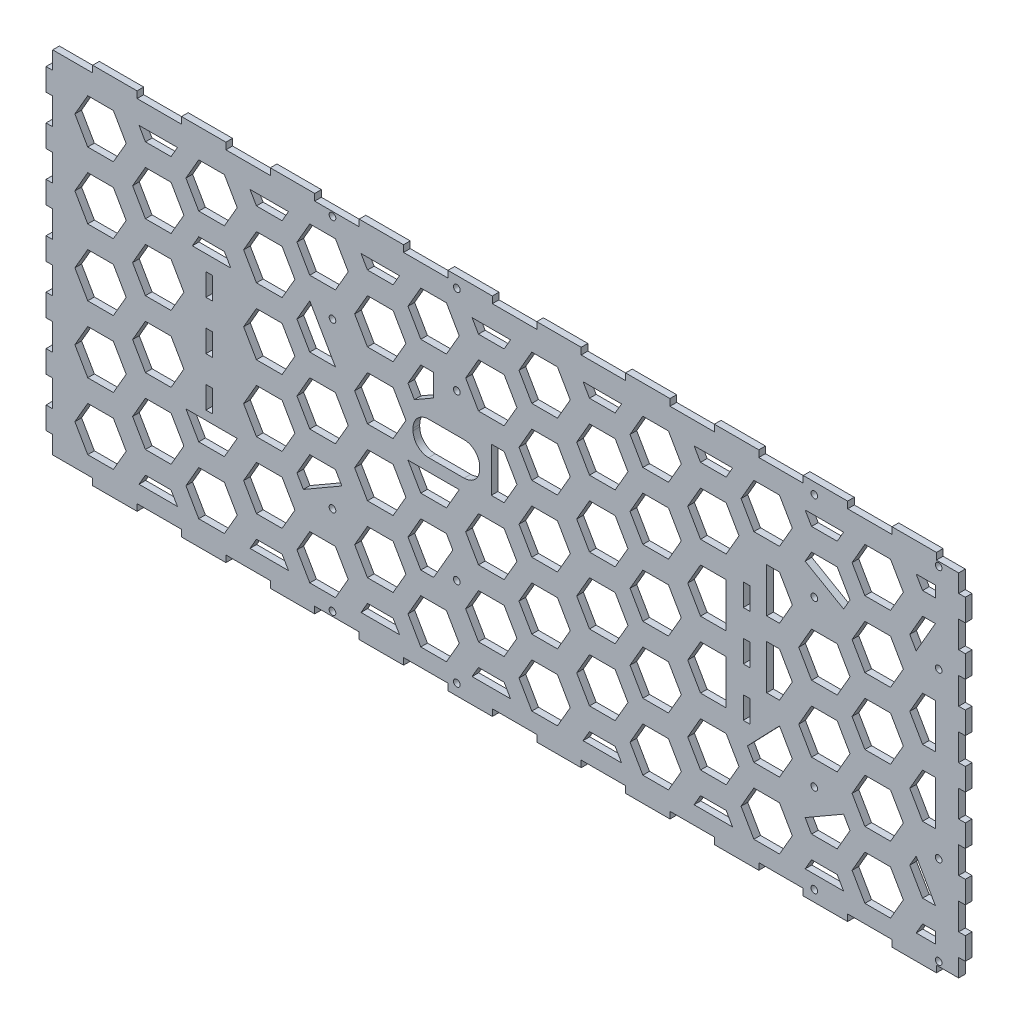
SolidWorks part; units mm, degrees
material "birch 3mm plywood"
ref_plane "Front Plane" through (0, 0, 0) normal (0, 0, 1) x (1, 0, 0)
ref_plane "Top Plane" through (0, 0, 0) normal (0, 1, 0) x (1, 0, 0)
ref_plane "Right Plane" through (0, 0, 0) normal (1, 0, 0) x (0, 0, -1)
sketch "Sketch1" plane through (0, 0, 152) normal (0, 0, 1) x (1, 0, 0)
  line L1 (-207, 82) -> (207, 82)
  line L2 (-207, 82) -> (-207, -82)
  line L3 (-207, -82) -> (207, -82)
  line L4 (207, 82) -> (207, -82)
  line L12 (200, -75) -> (-200, -75) construction
  line L13 (200, 75) -> (200, -75) construction
  line L14 (-200, -75) -> (-200, 75) construction
  line L15 (-200, 75) -> (200, 75) construction
  line L26 (-200, 0) -> (200, 0) construction
  line L31 (-200, 0) -> (200, 0) construction
  point P14 (0, 0)
  point P15 (0, 0)
  point P32 (-47.5, -25.9413)
  point P35 (256.981, -145.9413)
  point P38 (10.8894, 25.9413)
  point P51 (10.8894, -25.9413)
  point P54 (256.981, 145.9413)
  dimension "D1" = 7
  dimension "D2" = 7
  dimension "D3" = 7
  dimension "D4" = 7
  dimension "D5" = 150
  dimension "D6" = 400
extrude "Boss-Extrude1" add sketch "Sketch1" along normal blind 3
sketch "Sketch2" plane through (-207, 0, 0) normal (-1, 0, 0) x (0, 0, 1)
  line L7 (155, -82) -> (152, -82)
  line L8 (152, -82) -> (152, -71)
  line L9 (152, 82) -> (155, 82)
  line L10 (155, 82) -> (155, 71)
  line L11 (152, -61) -> (152, -49)
  line L12 (155, -71) -> (155, -82)
  line L13 (155, -49) -> (155, -61)
  line L14 (152, -39) -> (152, -27)
  line L15 (152, -17) -> (152, -5)
  line L16 (155, -27) -> (155, -39)
  line L17 (155, -5) -> (155, -17)
  line L18 (152, 5) -> (152, 17)
  line L19 (152, 27) -> (152, 39)
  line L20 (155, 17) -> (155, 5)
  line L21 (155, 39) -> (155, 27)
  line L22 (152, 49) -> (152, 61)
  line L23 (152, 71) -> (152, 82)
  line L24 (155, 61) -> (155, 49)
  line L76 (132.5, 88.6) -> (132.5, 93.6)
  line L77 (132.5, 88.6) -> (132.5, 93.6)
  line L78 (129.5, 98.6) -> (128.8771, 98.6)
  line L79 (129.5, 98.6) -> (128.8771, 98.6)
  line L80 (129.5, 82) -> (129.5, 88.6)
  line L81 (129.5, 82) -> (129.5, 88.6)
  line L82 (129.5, 88.6) -> (132.5, 88.6)
  line L83 (129.5, 88.6) -> (132.5, 88.6)
  line L85 (16, 82) -> (16, -82)
  line L102 (129.5, -82) -> (133, -82)
  line L103 (133, -82) -> (133, -79)
  line L104 (133, -79) -> (145, -79)
  line L105 (145, -79) -> (145, -82)
  line L106 (145, -82) -> (155, -82)
  line L107 (155, -82) -> (155, -71)
  line L108 (155, -71) -> (152, -71)
  line L109 (152, -71) -> (152, -61)
  line L110 (152, -61) -> (155, -61)
  line L111 (155, -61) -> (155, -49)
  line L112 (155, -49) -> (152, -49)
  line L113 (152, -49) -> (152, -39)
  line L114 (152, -39) -> (155, -39)
  line L115 (155, -39) -> (155, -27)
  line L116 (155, -27) -> (152, -27)
  line L117 (152, -27) -> (152, -17)
  line L118 (152, -17) -> (155, -17)
  line L119 (155, -17) -> (155, -5)
  line L120 (155, -5) -> (152, -5)
  line L121 (152, -5) -> (152, 5)
  line L122 (152, 5) -> (155, 5)
  line L123 (155, 5) -> (155, 17)
  line L124 (155, 17) -> (152, 17)
  line L125 (152, 17) -> (152, 27)
  line L126 (152, 27) -> (155, 27)
  line L127 (155, 27) -> (155, 39)
  line L128 (155, 39) -> (152, 39)
  line L129 (152, 39) -> (152, 49)
  line L130 (152, 49) -> (155, 49)
  line L131 (155, 49) -> (155, 61)
  line L132 (155, 61) -> (152, 61)
  line L133 (152, 61) -> (152, 71)
  line L134 (152, 71) -> (155, 71)
  line L135 (155, 71) -> (155, 82)
  line L136 (155, 82) -> (145, 82)
  line L137 (145, 82) -> (145, 79)
  line L138 (145, 79) -> (133, 79)
  line L139 (133, 79) -> (133, 82)
  line L140 (133, 82) -> (129.5, 82)
  line L184 (155, -71) -> (152, -71)
  line L186 (152, -61) -> (155, -61)
  line L188 (155, -49) -> (152, -49)
  line L190 (152, -39) -> (155, -39)
  line L192 (155, -27) -> (152, -27)
  line L194 (152, -17) -> (155, -17)
  line L196 (155, -5) -> (152, -5)
  line L198 (152, 5) -> (155, 5)
  line L200 (155, 17) -> (152, 17)
  line L202 (152, 27) -> (155, 27)
  line L204 (155, 39) -> (152, 39)
  line L206 (152, 49) -> (155, 49)
  line L208 (155, 61) -> (152, 61)
  line L210 (152, 71) -> (155, 71)
  line L297 (132.5, 93.6) -> (129.5, 93.6)
  line L298 (132.5, 93.6) -> (129.5, 93.6)
  line L299 (129.5, 93.6) -> (129.5, 98.6)
  line L300 (129.5, 93.6) -> (129.5, 98.6)
  line L301 (128.8771, -98.6) -> (129.5, -98.6)
  line L302 (128.8771, -98.6) -> (129.5, -98.6)
  line L303 (129.5, -98.6) -> (129.5, -93.6)
  line L304 (129.5, -98.6) -> (129.5, -93.6)
  line L305 (129.5, -93.6) -> (132.5, -93.6)
  line L306 (129.5, -93.6) -> (132.5, -93.6)
  line L307 (132.5, -93.6) -> (132.5, -88.6)
  line L308 (132.5, -93.6) -> (132.5, -88.6)
  line L309 (132.5, -88.6) -> (129.5, -88.6)
  line L310 (132.5, -88.6) -> (129.5, -88.6)
  line L311 (129.5, -88.6) -> (129.5, -82)
  line L312 (129.5, -88.6) -> (129.5, -82)
  arc A4 (128.8771, 98.6) -> (16, 82) centre (128.8771, -293.4723) ccw
  arc A5 (128.8771, 98.6) -> (16, 82) centre (128.8771, -293.4723) ccw
  arc A6 (16, -82) -> (128.8771, -98.6) centre (128.8771, 293.4723) ccw
  arc A7 (16, -82) -> (128.8771, -98.6) centre (128.8771, 293.4723) ccw
  line M77 (152, 82) -> (152, -82)
  line M78 (152, -82) -> (155, -82)
  line M79 (155, -82) -> (155, 82)
  line M80 (155, 82) -> (152, 82)
  dimension "D1" = 0
extrude "Cut-Extrude1" cut sketch "Sketch2" against normal blind 3 contours L184 M79 M77 M78 | L188 L186 M79 M77 | L192 L190 M79 M77 | L196 L194 M79 M77 | L200 L198 M79 M77 | L204 L202 M79 M77 | L208 L206 M79 M77 | L210 M77 M79 M80
mirror "Mirror1" about plane through (0, 0, 0) normal (1, 0, 0) of "Cut-Extrude1"
sketch "Sketch3" plane through (0, 82, 0) normal (0, 1, 0) x (1, 0, 0)
  line L92 (174, -152) -> (194, -152)
  line L93 (194, -152) -> (194, -155)
  line L94 (194, -155) -> (204, -155)
  line L97 (207, -45) -> (204, -45)
  line L120 (204, -16) -> (-204, -16)
  line L123 (-204, -45) -> (-207, -45)
  line L146 (-204, -155) -> (-186, -155)
  line L147 (-186, -155) -> (-186, -152)
  line L148 (-186, -152) -> (-166, -152)
  line L149 (-166, -152) -> (-166, -155)
  line L150 (-166, -155) -> (-146, -155)
  line L151 (-146, -155) -> (-146, -152)
  line L152 (-146, -152) -> (-126, -152)
  line L153 (-126, -152) -> (-126, -155)
  line L154 (-126, -155) -> (-106, -155)
  line L155 (-106, -155) -> (-106, -152)
  line L156 (-106, -152) -> (-86, -152)
  line L157 (-86, -152) -> (-86, -155)
  line L158 (-86, -155) -> (-66, -155)
  line L159 (-66, -155) -> (-66, -152)
  line L160 (-66, -152) -> (-46, -152)
  line L161 (-46, -152) -> (-46, -155)
  line L162 (-46, -155) -> (-26, -155)
  line L163 (-26, -155) -> (-26, -152)
  line L164 (-26, -152) -> (-6, -152)
  line L165 (-6, -152) -> (-6, -155)
  line L166 (-6, -155) -> (14, -155)
  line L167 (14, -155) -> (14, -152)
  line L168 (14, -152) -> (34, -152)
  line L169 (34, -152) -> (34, -155)
  line L170 (34, -155) -> (54, -155)
  line L171 (54, -155) -> (54, -152)
  line L172 (54, -152) -> (74, -152)
  line L173 (74, -152) -> (74, -155)
  line L174 (74, -155) -> (94, -155)
  line L175 (94, -155) -> (94, -152)
  line L176 (94, -152) -> (114, -152)
  line L177 (114, -152) -> (114, -155)
  line L178 (114, -155) -> (134, -155)
  line L179 (134, -155) -> (134, -152)
  line L180 (134, -152) -> (154, -152)
  line L181 (154, -152) -> (154, -155)
  line L182 (154, -155) -> (174, -155)
  line L183 (174, -155) -> (174, -152)
  line L184 (174, -152) -> (194, -152)
  line L185 (194, -152) -> (194, -155)
  line L186 (194, -155) -> (204, -155)
  line L212 (204, -16) -> (-204, -16)
  line L238 (-204, -155) -> (-186, -155)
  line L239 (-186, -155) -> (-186, -152)
  line L240 (-186, -152) -> (-166, -152)
  line L241 (-166, -152) -> (-166, -155)
  line L242 (-166, -155) -> (-146, -155)
  line L243 (-146, -155) -> (-146, -152)
  line L244 (-146, -152) -> (-126, -152)
  line L245 (-126, -152) -> (-126, -155)
  line L246 (-126, -155) -> (-106, -155)
  line L247 (-106, -155) -> (-106, -152)
  line L248 (-106, -152) -> (-86, -152)
  line L249 (-86, -152) -> (-86, -155)
  line L250 (-86, -155) -> (-66, -155)
  line L251 (-66, -155) -> (-66, -152)
  line L252 (-66, -152) -> (-46, -152)
  line L253 (-46, -152) -> (-46, -155)
  line L254 (-46, -155) -> (-26, -155)
  line L255 (-26, -155) -> (-26, -152)
  line L256 (-26, -152) -> (-6, -152)
  line L257 (-6, -152) -> (-6, -155)
  line L258 (-6, -155) -> (14, -155)
  line L259 (14, -155) -> (14, -152)
  line L260 (14, -152) -> (34, -152)
  line L261 (34, -152) -> (34, -155)
  line L262 (34, -155) -> (54, -155)
  line L263 (54, -155) -> (54, -152)
  line L264 (54, -152) -> (74, -152)
  line L265 (74, -152) -> (74, -155)
  line L266 (74, -155) -> (94, -155)
  line L267 (94, -155) -> (94, -152)
  line L268 (94, -152) -> (114, -152)
  line L269 (114, -152) -> (114, -155)
  line L270 (114, -155) -> (134, -155)
  line L271 (134, -155) -> (134, -152)
  line L272 (134, -152) -> (154, -152)
  line L273 (154, -152) -> (154, -155)
  line L274 (154, -155) -> (174, -155)
  line L275 (174, -155) -> (174, -152)
  line L576 (-204, -45) -> (-207, -45)
  line L577 (-207, -45) -> (-207, -57)
  line L578 (-207, -45) -> (-207, -57)
  line L579 (-207, -57) -> (-204, -57)
  line L580 (-207, -57) -> (-204, -57)
  line L581 (-204, -57) -> (-204, -67)
  line L582 (-204, -57) -> (-204, -67)
  line L583 (-204, -67) -> (-207, -67)
  line L584 (-204, -67) -> (-207, -67)
  line L585 (-207, -67) -> (-207, -79)
  line L586 (-207, -67) -> (-207, -79)
  line L587 (-207, -79) -> (-204, -79)
  line L588 (-207, -79) -> (-204, -79)
  line L589 (-204, -79) -> (-204, -89)
  line L590 (-204, -79) -> (-204, -89)
  line L591 (-204, -89) -> (-207, -89)
  line L592 (-204, -89) -> (-207, -89)
  line L593 (-207, -89) -> (-207, -101)
  line L594 (-207, -89) -> (-207, -101)
  line L595 (-207, -101) -> (-204, -101)
  line L596 (-207, -101) -> (-204, -101)
  line L597 (-204, -101) -> (-204, -111)
  line L598 (-204, -101) -> (-204, -111)
  line L599 (-204, -111) -> (-207, -111)
  line L600 (-204, -111) -> (-207, -111)
  line L601 (-207, -111) -> (-207, -123)
  line L602 (-207, -111) -> (-207, -123)
  line L603 (-207, -123) -> (-204, -123)
  line L604 (-207, -123) -> (-204, -123)
  line L605 (-204, -123) -> (-204, -133)
  line L606 (-204, -123) -> (-204, -133)
  line L607 (-204, -133) -> (-207, -133)
  line L608 (-204, -133) -> (-207, -133)
  line L609 (-207, -133) -> (-207, -145)
  line L610 (-207, -133) -> (-207, -145)
  line L611 (-207, -145) -> (-204, -145)
  line L612 (-207, -145) -> (-204, -145)
  line L613 (-204, -145) -> (-204, -155)
  line L614 (-204, -145) -> (-204, -155)
  line L615 (-204, -16) -> (-204, -23)
  line L616 (-204, -16) -> (-204, -23)
  line L617 (-204, -23) -> (-207, -23)
  line L618 (-204, -23) -> (-207, -23)
  line L619 (-207, -23) -> (-207, -35)
  line L620 (-207, -23) -> (-207, -35)
  line L621 (-207, -35) -> (-204, -35)
  line L622 (-207, -35) -> (-204, -35)
  line L623 (-204, -35) -> (-204, -45)
  line L624 (-204, -35) -> (-204, -45)
  line L741 (207, -45) -> (204, -45)
  line L742 (204, -45) -> (204, -35)
  line L743 (204, -45) -> (204, -35)
  line L744 (204, -35) -> (207, -35)
  line L745 (204, -35) -> (207, -35)
  line L746 (207, -35) -> (207, -23)
  line L747 (207, -35) -> (207, -23)
  line L748 (207, -23) -> (204, -23)
  line L749 (207, -23) -> (204, -23)
  line L750 (204, -23) -> (204, -16)
  line L751 (204, -23) -> (204, -16)
  line L752 (204, -155) -> (204, -145)
  line L753 (204, -155) -> (204, -145)
  line L754 (204, -145) -> (207, -145)
  line L755 (204, -145) -> (207, -145)
  line L756 (207, -145) -> (207, -133)
  line L757 (207, -145) -> (207, -133)
  line L758 (207, -133) -> (204, -133)
  line L759 (207, -133) -> (204, -133)
  line L760 (204, -133) -> (204, -123)
  line L761 (204, -133) -> (204, -123)
  line L762 (204, -123) -> (207, -123)
  line L763 (204, -123) -> (207, -123)
  line L764 (207, -123) -> (207, -111)
  line L765 (207, -123) -> (207, -111)
  line L766 (207, -111) -> (204, -111)
  line L767 (207, -111) -> (204, -111)
  line L768 (204, -111) -> (204, -101)
  line L769 (204, -111) -> (204, -101)
  line L770 (204, -101) -> (207, -101)
  line L771 (204, -101) -> (207, -101)
  line L772 (207, -101) -> (207, -89)
  line L773 (207, -101) -> (207, -89)
  line L774 (207, -89) -> (204, -89)
  line L775 (207, -89) -> (204, -89)
  line L776 (204, -89) -> (204, -79)
  line L777 (204, -89) -> (204, -79)
  line L778 (204, -79) -> (207, -79)
  line L779 (204, -79) -> (207, -79)
  line L780 (207, -79) -> (207, -67)
  line L781 (207, -79) -> (207, -67)
  line L782 (207, -67) -> (204, -67)
  line L783 (207, -67) -> (204, -67)
  line L784 (204, -67) -> (204, -57)
  line L785 (204, -67) -> (204, -57)
  line L786 (204, -57) -> (207, -57)
  line L787 (204, -57) -> (207, -57)
  line L788 (207, -57) -> (207, -45)
  line L789 (207, -57) -> (207, -45)
  dimension "D1" = 0
extrude "Cut-Extrude2" cut sketch "Sketch3" against normal blind 3
mirror "Mirror2" about plane through (0, 0, 0) normal (0, 1, 0) of "Cut-Extrude2"
sketch "Sketch4" plane through (0, 0, 155) normal (0, 0, 1) x (1, 0, 0)
  line L0 (-132, 27) -> (-132, 17) construction
  line L1 (-132, 17) -> (-135, 17) construction
  line L2 (-135, 17) -> (-135, 27) construction
  line L3 (-135, 27) -> (-132, 27) construction
  line L4 (-132, 5) -> (-132, -5) construction
  line L5 (-132, -5) -> (-135, -5) construction
  line L6 (-135, -5) -> (-135, 5) construction
  line L7 (-135, 5) -> (-132, 5) construction
  line L8 (-132, -17) -> (-132, -27) construction
  line L9 (-132, -27) -> (-135, -27) construction
  line L10 (-135, -27) -> (-135, -17) construction
  line L11 (-135, -17) -> (-132, -17) construction
  line L12 (-132, 27) -> (-132, 17)
  line L13 (-132, 17) -> (-135, 17)
  line L14 (-135, 17) -> (-135, 27)
  line L15 (-135, 27) -> (-132, 27)
  line L16 (-132, 5) -> (-132, -5)
  line L17 (-132, -5) -> (-135, -5)
  line L18 (-135, -5) -> (-135, 5)
  line L19 (-135, 5) -> (-132, 5)
  line L20 (-132, -17) -> (-132, -27)
  line L21 (-132, -27) -> (-135, -27)
  line L22 (-135, -27) -> (-135, -17)
  line L23 (-135, -17) -> (-132, -17)
  line L24 (110, 27) -> (110, 17) construction
  line L25 (110, 17) -> (107, 17) construction
  line L26 (107, 17) -> (107, 27) construction
  line L27 (107, 27) -> (110, 27) construction
  line L28 (110, 5) -> (110, -5) construction
  line L29 (110, -5) -> (107, -5) construction
  line L30 (107, -5) -> (107, 5) construction
  line L31 (107, 5) -> (110, 5) construction
  line L32 (110, -17) -> (110, -27) construction
  line L33 (110, -27) -> (107, -27) construction
  line L34 (107, -27) -> (107, -17) construction
  line L35 (107, -17) -> (110, -17) construction
  line L36 (110, 27) -> (110, 17)
  line L37 (110, 17) -> (107, 17)
  line L38 (107, 17) -> (107, 27)
  line L39 (107, 27) -> (110, 27)
  line L40 (110, 5) -> (110, -5)
  line L41 (110, -5) -> (107, -5)
  line L42 (107, -5) -> (107, 5)
  line L43 (107, 5) -> (110, 5)
  line L44 (110, -17) -> (110, -27)
  line L45 (110, -27) -> (107, -27)
  line L46 (107, -27) -> (107, -17)
  line L47 (107, -17) -> (110, -17)
  line L80 (207, 0) -> (-207, 0) construction
  line L81 (207, -5) -> (207, 5) construction
  line L82 (-207, 5) -> (-207, -5) construction
  circle A0 centre (139, 37) radius 1.5 construction
  circle A1 centre (195, 37) radius 1.5 construction
  circle A2 centre (195, 77) radius 1.5 construction
  circle A3 centre (139, 77) radius 1.5 construction
  circle A4 centre (-78, 77) radius 1.5 construction
  circle A5 centre (-22, 77) radius 1.5 construction
  circle A6 centre (-78, 37) radius 1.5 construction
  circle A7 centre (-22, 37) radius 1.5 construction
  circle A8 centre (139, 37) radius 1.5
  circle A9 centre (195, 37) radius 1.5
  circle A10 centre (195, 77) radius 1.5
  circle A11 centre (139, 77) radius 1.5
  circle A12 centre (-78, 77) radius 1.5
  circle A13 centre (-22, 77) radius 1.5
  circle A14 centre (-78, 37) radius 1.5
  circle A15 centre (-22, 37) radius 1.5
  circle A16 centre (139, -77) radius 1.5
  circle A17 centre (195, -77) radius 1.5
  circle A18 centre (195, -37) radius 1.5
  circle A19 centre (139, -37) radius 1.5
  circle A20 centre (-22, -37) radius 1.5
  circle A21 centre (-78, -37) radius 1.5
  circle A22 centre (-22, -77) radius 1.5
  circle A23 centre (-78, -77) radius 1.5
extrude "Cut-Extrude3" cut sketch "Sketch4" against normal blind 10
sketch "Sketch5" plane through (0, 0, 155) normal (0, 0, 1) x (1, 0, 0)
  line L1 (-34.7, 4.6) -> (-18.7, 4.6)
  line L2 (-41.7, 11.6) -> (-41.7, 12.6)
  line L3 (-34.7, 19.6) -> (-18.7, 19.6)
  line L4 (-11.7, 12.6) -> (-11.7, 11.6)
  line L5 (-27.7, 4.6) -> (0, 4.6) construction
  line L7 (-27.7, 4.6) -> (-27.7, -7.8) construction
  arc A0 (-34.7, 19.6) -> (-41.7, 12.6) centre (-34.7, 12.6) ccw
  arc A1 (-11.7, 12.6) -> (-18.7, 19.6) centre (-18.7, 12.6) ccw
  arc A2 (-18.7, 4.6) -> (-11.7, 11.6) centre (-18.7, 11.6) ccw
  arc A3 (-34.7, 4.6) -> (-41.7, 11.6) centre (-34.7, 11.6) cw
  point P16 (-11.7, 4.6)
  point P19 (-41.7, 4.6)
  dimension "D4" = 7
  dimension "D1" = 30
  dimension "D2" = 15
  dimension "D3" = 16
extrude "Cut-Extrude4" cut sketch "Sketch5" against normal blind 10
sketch "Sketch6" plane through (0, 0, 155) normal (0, 0, 1) x (1, 0, 0)
  line L0 (-204, 79) -> (-186, 79) construction
  line L1 (-170.906, 59) -> (-176.6795, 69)
  line L2 (-176.6795, 69) -> (-188.2265, 69)
  line L3 (-188.2265, 69) -> (-194, 59)
  line L4 (-194, 59) -> (-188.2265, 49)
  line L5 (-188.2265, 49) -> (-176.6795, 49)
  line L6 (-176.6795, 49) -> (-170.906, 59)
  line L7 (-204, 49) -> (-204, 61) construction
  line L8 (-144.9252, 44) -> (-150.6987, 54)
  line L9 (-150.6987, 54) -> (-162.2457, 54)
  line L10 (-162.2457, 54) -> (-168.0192, 44)
  line L11 (-168.0192, 44) -> (-162.2457, 34)
  line L12 (-162.2457, 34) -> (-150.6987, 34)
  line L13 (-150.6987, 34) -> (-144.9252, 44)
  line L14 (-120.906, 59) -> (-126.6795, 69)
  line L15 (-126.6795, 69) -> (-138.2265, 69)
  line L16 (-138.2265, 69) -> (-144, 59)
  line L17 (-144, 59) -> (-138.2265, 49)
  line L18 (-138.2265, 49) -> (-126.6795, 49)
  line L19 (-126.6795, 49) -> (-120.906, 59)
  line L20 (-94.9252, 44) -> (-100.6987, 54)
  line L21 (-100.6987, 54) -> (-112.2457, 54)
  line L22 (-112.2457, 54) -> (-118.0192, 44)
  line L23 (-118.0192, 44) -> (-112.2457, 34)
  line L24 (-112.2457, 34) -> (-100.6987, 34)
  line L25 (-100.6987, 34) -> (-94.9252, 44)
  line L26 (-70.906, 59) -> (-76.6795, 69)
  line L27 (-76.6795, 69) -> (-88.2265, 69)
  line L28 (-88.2265, 69) -> (-94, 59)
  line L29 (-94, 59) -> (-88.2265, 49)
  line L30 (-88.2265, 49) -> (-76.6795, 49)
  line L31 (-76.6795, 49) -> (-70.906, 59)
  line L32 (-44.9252, 44) -> (-50.6987, 54)
  line L33 (-50.6987, 54) -> (-62.2457, 54)
  line L34 (-62.2457, 54) -> (-68.0192, 44)
  line L35 (-68.0192, 44) -> (-62.2457, 34)
  line L36 (-62.2457, 34) -> (-50.6987, 34)
  line L37 (-50.6987, 34) -> (-44.9252, 44)
  line L38 (-20.906, 59) -> (-26.6795, 69)
  line L39 (-26.6795, 69) -> (-38.2265, 69)
  line L40 (-38.2265, 69) -> (-44, 59)
  line L41 (-44, 59) -> (-38.2265, 49)
  line L42 (-38.2265, 49) -> (-26.6795, 49)
  line L43 (-26.6795, 49) -> (-20.906, 59)
  line L44 (5.0748, 44) -> (-0.6987, 54)
  line L45 (-0.6987, 54) -> (-12.2457, 54)
  line L46 (-12.2457, 54) -> (-18.0192, 44)
  line L47 (-18.0192, 44) -> (-12.2457, 34)
  line L48 (-12.2457, 34) -> (-0.6987, 34)
  line L49 (-0.6987, 34) -> (5.0748, 44)
  line L50 (29.094, 59) -> (23.3205, 69)
  line L51 (23.3205, 69) -> (11.7735, 69)
  line L52 (11.7735, 69) -> (6, 59)
  line L53 (6, 59) -> (11.7735, 49)
  line L54 (11.7735, 49) -> (23.3205, 49)
  line L55 (23.3205, 49) -> (29.094, 59)
  line L56 (55.0748, 44) -> (49.3013, 54)
  line L57 (49.3013, 54) -> (37.7543, 54)
  line L58 (37.7543, 54) -> (31.9808, 44)
  line L59 (31.9808, 44) -> (37.7543, 34)
  line L60 (37.7543, 34) -> (49.3013, 34)
  line L61 (49.3013, 34) -> (55.0748, 44)
  line L62 (79.094, 59) -> (73.3205, 69)
  line L63 (73.3205, 69) -> (61.7735, 69)
  line L64 (61.7735, 69) -> (56, 59)
  line L65 (56, 59) -> (61.7735, 49)
  line L66 (61.7735, 49) -> (73.3205, 49)
  line L67 (73.3205, 49) -> (79.094, 59)
  line L68 (105.0748, 44) -> (99.3013, 54)
  line L69 (99.3013, 54) -> (87.7543, 54)
  line L70 (87.7543, 54) -> (81.9808, 44)
  line L71 (81.9808, 44) -> (87.7543, 34)
  line L72 (87.7543, 34) -> (99.3013, 34)
  line L73 (99.3013, 34) -> (105.0748, 44)
  line L74 (129.094, 59) -> (123.3205, 69)
  line L75 (123.3205, 69) -> (111.7735, 69)
  line L76 (111.7735, 69) -> (106, 59)
  line L77 (106, 59) -> (111.7735, 49)
  line L78 (111.7735, 49) -> (123.3205, 49)
  line L79 (123.3205, 49) -> (129.094, 59)
  line L80 (155.0748, 44) -> (149.3013, 54)
  line L81 (149.3013, 54) -> (137.7543, 54)
  line L82 (137.7543, 54) -> (134.8675, 49)
  line L85 (152.188, 39) -> (155.0748, 44)
  line L86 (179.094, 59) -> (173.3205, 69)
  line L87 (173.3205, 69) -> (161.7735, 69)
  line L88 (161.7735, 69) -> (156, 59)
  line L89 (156, 59) -> (161.7735, 49)
  line L90 (161.7735, 49) -> (173.3205, 49)
  line L91 (173.3205, 49) -> (179.094, 59)
  line L93 (193.5278, 54) -> (187.7543, 54)
  line L94 (187.7543, 54) -> (181.9808, 44)
  line L95 (181.9808, 44) -> (184.8675, 39)
  line L98 (-123.7927, 34) -> (-126.6795, 39)
  line L99 (-126.6795, 39) -> (-138.2265, 39)
  line L100 (-138.2265, 39) -> (-141.1132, 34)
  line L104 (-94.9252, 14) -> (-100.6987, 24)
  line L105 (-100.6987, 24) -> (-112.2457, 24)
  line L106 (-112.2457, 24) -> (-118.0192, 14)
  line L107 (-118.0192, 14) -> (-112.2457, 4)
  line L108 (-112.2457, 4) -> (-100.6987, 4)
  line L109 (-100.6987, 4) -> (-94.9252, 14)
  line L112 (-88.2265, 39) -> (-94, 29)
  line L113 (-94, 29) -> (-88.2265, 19)
  line L114 (-88.2265, 19) -> (-76.6795, 19)
  line L116 (-44.9252, 14) -> (-50.6987, 24)
  line L117 (-50.6987, 24) -> (-62.2457, 24)
  line L118 (-62.2457, 24) -> (-68.0192, 14)
  line L119 (-68.0192, 14) -> (-62.2457, 4)
  line L120 (-62.2457, 4) -> (-50.6987, 4)
  line L121 (-50.6987, 4) -> (-44.9252, 14)
  line L123 (-32.453, 39) -> (-38.2265, 39)
  line L124 (-38.2265, 39) -> (-44, 29)
  line L125 (-44, 29) -> (-41.1132, 24)
  line L128 (5.0748, 14) -> (-0.6987, 24)
  line L129 (-0.6987, 24) -> (-6.4722, 24)
  line L132 (-6.4722, 4) -> (-0.6987, 4)
  line L133 (-0.6987, 4) -> (5.0748, 14)
  line L134 (29.094, 29) -> (23.3205, 39)
  line L135 (23.3205, 39) -> (11.7735, 39)
  line L136 (11.7735, 39) -> (6, 29)
  line L137 (6, 29) -> (11.7735, 19)
  line L138 (11.7735, 19) -> (23.3205, 19)
  line L139 (23.3205, 19) -> (29.094, 29)
  line L140 (55.0748, 14) -> (49.3013, 24)
  line L141 (49.3013, 24) -> (37.7543, 24)
  line L142 (37.7543, 24) -> (31.9808, 14)
  line L143 (31.9808, 14) -> (37.7543, 4)
  line L144 (37.7543, 4) -> (49.3013, 4)
  line L145 (49.3013, 4) -> (55.0748, 14)
  line L146 (79.094, 29) -> (73.3205, 39)
  line L147 (73.3205, 39) -> (61.7735, 39)
  line L148 (61.7735, 39) -> (56, 29)
  line L149 (56, 29) -> (61.7735, 19)
  line L150 (61.7735, 19) -> (73.3205, 19)
  line L151 (73.3205, 19) -> (79.094, 29)
  line L153 (99.3013, 24) -> (87.7543, 24)
  line L154 (87.7543, 24) -> (81.9808, 14)
  line L155 (81.9808, 14) -> (87.7543, 4)
  line L156 (87.7543, 4) -> (99.3013, 4)
  line L158 (129.094, 29) -> (123.3205, 39)
  line L159 (123.3205, 39) -> (117.547, 39)
  line L162 (117.547, 19) -> (123.3205, 19)
  line L163 (123.3205, 19) -> (129.094, 29)
  line L164 (155.0748, 14) -> (149.3013, 24)
  line L165 (149.3013, 24) -> (137.7543, 24)
  line L166 (137.7543, 24) -> (131.9808, 14)
  line L167 (131.9808, 14) -> (137.7543, 4)
  line L168 (137.7543, 4) -> (149.3013, 4)
  line L169 (149.3013, 4) -> (155.0748, 14)
  line L170 (179.094, 29) -> (173.3205, 39)
  line L171 (173.3205, 39) -> (161.7735, 39)
  line L172 (161.7735, 39) -> (156, 29)
  line L173 (156, 29) -> (161.7735, 19)
  line L174 (161.7735, 19) -> (173.3205, 19)
  line L175 (173.3205, 19) -> (179.094, 29)
  line L177 (193.5278, 24) -> (187.7543, 24)
  line L178 (187.7543, 24) -> (181.9808, 14)
  line L179 (181.9808, 14) -> (187.7543, 4)
  line L180 (187.7543, 4) -> (193.5278, 4)
  line L188 (-94.9252, -16) -> (-100.6987, -6)
  line L189 (-100.6987, -6) -> (-112.2457, -6)
  line L190 (-112.2457, -6) -> (-118.0192, -16)
  line L191 (-118.0192, -16) -> (-112.2457, -26)
  line L192 (-112.2457, -26) -> (-100.6987, -26)
  line L193 (-100.6987, -26) -> (-94.9252, -16)
  line L194 (-70.906, -1) -> (-76.6795, 9)
  line L195 (-76.6795, 9) -> (-88.2265, 9)
  line L196 (-88.2265, 9) -> (-94, -1)
  line L197 (-94, -1) -> (-88.2265, -11)
  line L198 (-88.2265, -11) -> (-76.6795, -11)
  line L199 (-76.6795, -11) -> (-70.906, -1)
  line L200 (-44.9252, -16) -> (-50.6987, -6)
  line L201 (-50.6987, -6) -> (-62.2457, -6)
  line L202 (-62.2457, -6) -> (-68.0192, -16)
  line L203 (-68.0192, -16) -> (-62.2457, -26)
  line L204 (-62.2457, -26) -> (-50.6987, -26)
  line L205 (-50.6987, -26) -> (-44.9252, -16)
  line L209 (-44, -1) -> (-38.2265, -11)
  line L210 (-38.2265, -11) -> (-26.6795, -11)
  line L211 (-26.6795, -11) -> (-20.906, -1)
  line L212 (5.0748, -16) -> (-0.6987, -6)
  line L213 (-0.6987, -6) -> (-12.2457, -6)
  line L214 (-12.2457, -6) -> (-18.0192, -16)
  line L215 (-18.0192, -16) -> (-12.2457, -26)
  line L216 (-12.2457, -26) -> (-0.6987, -26)
  line L217 (-0.6987, -26) -> (5.0748, -16)
  line L218 (29.094, -1) -> (23.3205, 9)
  line L219 (23.3205, 9) -> (11.7735, 9)
  line L220 (11.7735, 9) -> (6, -1)
  line L221 (6, -1) -> (11.7735, -11)
  line L222 (11.7735, -11) -> (23.3205, -11)
  line L223 (23.3205, -11) -> (29.094, -1)
  line L224 (55.0748, -16) -> (49.3013, -6)
  line L225 (49.3013, -6) -> (37.7543, -6)
  line L226 (37.7543, -6) -> (31.9808, -16)
  line L227 (31.9808, -16) -> (37.7543, -26)
  line L228 (37.7543, -26) -> (49.3013, -26)
  line L229 (49.3013, -26) -> (55.0748, -16)
  line L230 (79.094, -1) -> (73.3205, 9)
  line L231 (73.3205, 9) -> (61.7735, 9)
  line L232 (61.7735, 9) -> (56, -1)
  line L233 (56, -1) -> (61.7735, -11)
  line L234 (61.7735, -11) -> (73.3205, -11)
  line L235 (73.3205, -11) -> (79.094, -1)
  line L237 (99.3013, -6) -> (87.7543, -6)
  line L238 (87.7543, -6) -> (81.9808, -16)
  line L239 (81.9808, -16) -> (87.7543, -26)
  line L240 (87.7543, -26) -> (99.3013, -26)
  line L242 (129.094, -1) -> (123.3205, 9)
  line L243 (123.3205, 9) -> (117.547, 9)
  line L246 (117.547, -11) -> (123.3205, -11)
  line L247 (123.3205, -11) -> (129.094, -1)
  line L248 (155.0748, -16) -> (149.3013, -6)
  line L249 (149.3013, -6) -> (137.7543, -6)
  line L250 (137.7543, -6) -> (131.9808, -16)
  line L251 (131.9808, -16) -> (137.7543, -26)
  line L252 (137.7543, -26) -> (149.3013, -26)
  line L253 (149.3013, -26) -> (155.0748, -16)
  line L254 (179.094, -1) -> (173.3205, 9)
  line L255 (173.3205, 9) -> (161.7735, 9)
  line L256 (161.7735, 9) -> (156, -1)
  line L257 (156, -1) -> (161.7735, -11)
  line L258 (161.7735, -11) -> (173.3205, -11)
  line L259 (173.3205, -11) -> (179.094, -1)
  line L261 (193.5278, -6) -> (187.7543, -6)
  line L262 (187.7543, -6) -> (181.9808, -16)
  line L263 (181.9808, -16) -> (187.7543, -26)
  line L264 (187.7543, -26) -> (193.5278, -26)
  line L269 (-144, -31) -> (-138.2265, -41)
  line L270 (-138.2265, -41) -> (-126.6795, -41)
  line L271 (-126.6795, -41) -> (-120.906, -31)
  line L272 (-94.9252, -46) -> (-100.6987, -36)
  line L273 (-100.6987, -36) -> (-112.2457, -36)
  line L274 (-112.2457, -36) -> (-118.0192, -46)
  line L275 (-118.0192, -46) -> (-112.2457, -56)
  line L276 (-112.2457, -56) -> (-100.6987, -56)
  line L277 (-100.6987, -56) -> (-94.9252, -46)
  line L278 (-73.7927, -26) -> (-76.6795, -21)
  line L279 (-76.6795, -21) -> (-88.2265, -21)
  line L280 (-88.2265, -21) -> (-94, -31)
  line L281 (-94, -31) -> (-91.1132, -36)
  line L284 (-44.9252, -46) -> (-50.6987, -36)
  line L285 (-50.6987, -36) -> (-62.2457, -36)
  line L286 (-62.2457, -36) -> (-68.0192, -46)
  line L287 (-68.0192, -46) -> (-62.2457, -56)
  line L288 (-62.2457, -56) -> (-50.6987, -56)
  line L289 (-50.6987, -56) -> (-44.9252, -46)
  line L290 (-23.7927, -26) -> (-26.6795, -21)
  line L291 (-26.6795, -21) -> (-38.2265, -21)
  line L292 (-38.2265, -21) -> (-44, -31)
  line L293 (-44, -31) -> (-38.2265, -41)
  line L294 (-38.2265, -41) -> (-32.453, -41)
  line L296 (5.0748, -46) -> (-0.6987, -36)
  line L297 (-0.6987, -36) -> (-12.2457, -36)
  line L298 (-12.2457, -36) -> (-18.0192, -46)
  line L299 (-18.0192, -46) -> (-12.2457, -56)
  line L300 (-12.2457, -56) -> (-0.6987, -56)
  line L301 (-0.6987, -56) -> (5.0748, -46)
  line L302 (29.094, -31) -> (23.3205, -21)
  line L303 (23.3205, -21) -> (11.7735, -21)
  line L304 (11.7735, -21) -> (6, -31)
  line L305 (6, -31) -> (11.7735, -41)
  line L306 (11.7735, -41) -> (23.3205, -41)
  line L307 (23.3205, -41) -> (29.094, -31)
  line L308 (55.0748, -46) -> (49.3013, -36)
  line L309 (49.3013, -36) -> (37.7543, -36)
  line L310 (37.7543, -36) -> (31.9808, -46)
  line L311 (31.9808, -46) -> (37.7543, -56)
  line L312 (37.7543, -56) -> (49.3013, -56)
  line L313 (49.3013, -56) -> (55.0748, -46)
  line L314 (79.094, -31) -> (73.3205, -21)
  line L315 (73.3205, -21) -> (61.7735, -21)
  line L316 (61.7735, -21) -> (56, -31)
  line L317 (56, -31) -> (61.7735, -41)
  line L318 (61.7735, -41) -> (73.3205, -41)
  line L319 (73.3205, -41) -> (79.094, -31)
  line L320 (105.0748, -46) -> (99.3013, -36)
  line L321 (99.3013, -36) -> (87.7543, -36)
  line L322 (87.7543, -36) -> (81.9808, -46)
  line L323 (81.9808, -46) -> (87.7543, -56)
  line L324 (87.7543, -56) -> (99.3013, -56)
  line L325 (99.3013, -56) -> (105.0748, -46)
  line L326 (129.094, -31) -> (123.3205, -21)
  line L329 (108.8868, -36) -> (111.7735, -41)
  line L330 (111.7735, -41) -> (123.3205, -41)
  line L331 (123.3205, -41) -> (129.094, -31)
  line L332 (155.0748, -46) -> (152.188, -41)
  line L335 (134.8675, -51) -> (137.7543, -56)
  line L336 (137.7543, -56) -> (149.3013, -56)
  line L337 (149.3013, -56) -> (155.0748, -46)
  line L338 (179.094, -31) -> (173.3205, -21)
  line L339 (173.3205, -21) -> (161.7735, -21)
  line L340 (161.7735, -21) -> (156, -31)
  line L341 (156, -31) -> (161.7735, -41)
  line L342 (161.7735, -41) -> (173.3205, -41)
  line L343 (173.3205, -41) -> (179.094, -31)
  line L346 (184.8675, -41) -> (181.9808, -46)
  line L347 (181.9808, -46) -> (187.7543, -56)
  line L348 (187.7543, -56) -> (193.5278, -56)
  line L350 (-120.906, -61) -> (-126.6795, -51)
  line L351 (-126.6795, -51) -> (-138.2265, -51)
  line L352 (-138.2265, -51) -> (-144, -61)
  line L353 (-144, -61) -> (-138.2265, -71)
  line L354 (-138.2265, -71) -> (-126.6795, -71)
  line L355 (-126.6795, -71) -> (-120.906, -61)
  line L362 (-70.906, -61) -> (-76.6795, -51)
  line L363 (-76.6795, -51) -> (-88.2265, -51)
  line L364 (-88.2265, -51) -> (-94, -61)
  line L365 (-94, -61) -> (-88.2265, -71)
  line L366 (-88.2265, -71) -> (-76.6795, -71)
  line L367 (-76.6795, -71) -> (-70.906, -61)
  line L374 (-20.906, -61) -> (-26.6795, -51)
  line L375 (-26.6795, -51) -> (-38.2265, -51)
  line L376 (-38.2265, -51) -> (-44, -61)
  line L377 (-44, -61) -> (-38.2265, -71)
  line L378 (-38.2265, -71) -> (-26.6795, -71)
  line L379 (-26.6795, -71) -> (-20.906, -61)
  line L386 (29.094, -61) -> (23.3205, -51)
  line L387 (23.3205, -51) -> (11.7735, -51)
  line L388 (11.7735, -51) -> (6, -61)
  line L389 (6, -61) -> (11.7735, -71)
  line L390 (11.7735, -71) -> (23.3205, -71)
  line L391 (23.3205, -71) -> (29.094, -61)
  line L398 (79.094, -61) -> (73.3205, -51)
  line L399 (73.3205, -51) -> (61.7735, -51)
  line L400 (61.7735, -51) -> (56, -61)
  line L401 (56, -61) -> (61.7735, -71)
  line L402 (61.7735, -71) -> (73.3205, -71)
  line L403 (73.3205, -71) -> (79.094, -61)
  line L410 (129.094, -61) -> (123.3205, -51)
  line L411 (123.3205, -51) -> (111.7735, -51)
  line L412 (111.7735, -51) -> (106, -61)
  line L413 (106, -61) -> (111.7735, -71)
  line L414 (111.7735, -71) -> (123.3205, -71)
  line L415 (123.3205, -71) -> (129.094, -61)
  line L422 (179.094, -61) -> (173.3205, -51)
  line L423 (173.3205, -51) -> (161.7735, -51)
  line L424 (161.7735, -51) -> (156, -61)
  line L425 (156, -61) -> (161.7735, -71)
  line L426 (161.7735, -71) -> (173.3205, -71)
  line L427 (173.3205, -71) -> (179.094, -61)
  line L434 (-170.906, 29) -> (-176.6795, 39)
  line L435 (-176.6795, 39) -> (-188.2265, 39)
  line L436 (-188.2265, 39) -> (-194, 29)
  line L437 (-194, 29) -> (-188.2265, 19)
  line L438 (-188.2265, 19) -> (-176.6795, 19)
  line L439 (-176.6795, 19) -> (-170.906, 29)
  line L440 (-144.9252, 14) -> (-150.6987, 24)
  line L441 (-150.6987, 24) -> (-162.2457, 24)
  line L442 (-162.2457, 24) -> (-168.0192, 14)
  line L443 (-168.0192, 14) -> (-162.2457, 4)
  line L444 (-162.2457, 4) -> (-150.6987, 4)
  line L445 (-150.6987, 4) -> (-144.9252, 14)
  line L446 (-170.906, -1) -> (-176.6795, 9)
  line L447 (-176.6795, 9) -> (-188.2265, 9)
  line L448 (-188.2265, 9) -> (-194, -1)
  line L449 (-194, -1) -> (-188.2265, -11)
  line L450 (-188.2265, -11) -> (-176.6795, -11)
  line L451 (-176.6795, -11) -> (-170.906, -1)
  line L452 (-144.9252, -16) -> (-150.6987, -6)
  line L453 (-150.6987, -6) -> (-162.2457, -6)
  line L454 (-162.2457, -6) -> (-168.0192, -16)
  line L455 (-168.0192, -16) -> (-162.2457, -26)
  line L456 (-162.2457, -26) -> (-150.6987, -26)
  line L457 (-150.6987, -26) -> (-144.9252, -16)
  line L458 (-170.906, -31) -> (-176.6795, -21)
  line L459 (-176.6795, -21) -> (-188.2265, -21)
  line L460 (-188.2265, -21) -> (-194, -31)
  line L461 (-194, -31) -> (-188.2265, -41)
  line L462 (-188.2265, -41) -> (-176.6795, -41)
  line L463 (-176.6795, -41) -> (-170.906, -31)
  line L464 (-144.9252, -46) -> (-150.6987, -36)
  line L465 (-150.6987, -36) -> (-162.2457, -36)
  line L466 (-162.2457, -36) -> (-168.0192, -46)
  line L467 (-168.0192, -46) -> (-162.2457, -56)
  line L468 (-162.2457, -56) -> (-150.6987, -56)
  line L469 (-150.6987, -56) -> (-144.9252, -46)
  line L470 (-170.906, -61) -> (-176.6795, -51)
  line L471 (-176.6795, -51) -> (-188.2265, -51)
  line L472 (-188.2265, -51) -> (-194, -61)
  line L473 (-194, -61) -> (-188.2265, -71)
  line L474 (-188.2265, -71) -> (-176.6795, -71)
  line L475 (-176.6795, -71) -> (-170.906, -61)
  line L482 (-144.9252, -76) -> (-150.6987, -66) [skipped]
  line L483 (-150.6987, -66) -> (-162.2457, -66) [skipped]
  line L484 (-162.2457, -66) -> (-168.0192, -76) [skipped]
  line L485 (-168.0192, -76) -> (-162.2457, -86) [skipped]
  line L486 (-162.2457, -86) -> (-150.6987, -86) [skipped]
  line L487 (-150.6987, -86) -> (-144.9252, -76) [skipped]
  line L488 (-94.9252, -76) -> (-100.6987, -66) [skipped]
  line L489 (-100.6987, -66) -> (-112.2457, -66) [skipped]
  line L490 (-112.2457, -66) -> (-118.0192, -76) [skipped]
  line L491 (-118.0192, -76) -> (-112.2457, -86) [skipped]
  line L492 (-112.2457, -86) -> (-100.6987, -86) [skipped]
  line L493 (-100.6987, -86) -> (-94.9252, -76) [skipped]
  line L494 (-44.9252, -76) -> (-50.6987, -66) [skipped]
  line L495 (-50.6987, -66) -> (-62.2457, -66) [skipped]
  line L496 (-62.2457, -66) -> (-68.0192, -76) [skipped]
  line L497 (-68.0192, -76) -> (-62.2457, -86) [skipped]
  line L498 (-62.2457, -86) -> (-50.6987, -86) [skipped]
  line L499 (-50.6987, -86) -> (-44.9252, -76) [skipped]
  line L500 (5.0748, -76) -> (-0.6987, -66) [skipped]
  line L501 (-0.6987, -66) -> (-12.2457, -66) [skipped]
  line L502 (-12.2457, -66) -> (-18.0192, -76) [skipped]
  line L503 (-18.0192, -76) -> (-12.2457, -86) [skipped]
  line L504 (-12.2457, -86) -> (-0.6987, -86) [skipped]
  line L505 (-0.6987, -86) -> (5.0748, -76) [skipped]
  line L506 (55.0748, -76) -> (49.3013, -66) [skipped]
  line L507 (49.3013, -66) -> (37.7543, -66) [skipped]
  line L508 (37.7543, -66) -> (31.9808, -76) [skipped]
  line L509 (31.9808, -76) -> (37.7543, -86) [skipped]
  line L510 (37.7543, -86) -> (49.3013, -86) [skipped]
  line L511 (49.3013, -86) -> (55.0748, -76) [skipped]
  line L512 (105.0748, -76) -> (99.3013, -66) [skipped]
  line L513 (99.3013, -66) -> (87.7543, -66) [skipped]
  line L514 (87.7543, -66) -> (81.9808, -76) [skipped]
  line L515 (81.9808, -76) -> (87.7543, -86) [skipped]
  line L516 (87.7543, -86) -> (99.3013, -86) [skipped]
  line L517 (99.3013, -86) -> (105.0748, -76) [skipped]
  line L518 (155.0748, -76) -> (149.3013, -66) [skipped]
  line L519 (149.3013, -66) -> (137.7543, -66) [skipped]
  line L520 (137.7543, -66) -> (131.9808, -76) [skipped]
  line L521 (131.9808, -76) -> (137.7543, -86) [skipped]
  line L522 (137.7543, -86) -> (149.3013, -86) [skipped]
  line L523 (149.3013, -86) -> (155.0748, -76) [skipped]
  line L524 (205.0748, -76) -> (199.3013, -66) [skipped]
  line L525 (199.3013, -66) -> (187.7543, -66) [skipped]
  line L526 (187.7543, -66) -> (181.9808, -76) [skipped]
  line L527 (181.9808, -76) -> (187.7543, -86) [skipped]
  line L528 (187.7543, -86) -> (199.3013, -86) [skipped]
  line L529 (199.3013, -86) -> (205.0748, -76) [skipped]
  line L530 (-120.906, -1) -> (-126.6795, 9) [skipped]
  line L531 (-138.2265, 9) -> (-144, -1) [skipped]
  line L532 (-144, -1) -> (-138.2265, -11) [skipped]
  line L533 (-126.6795, -11) -> (-120.906, -1) [skipped]
  line L534 (-126.6795, 9) -> (-138.2265, 9) [skipped]
  line L535 (-138.2265, -11) -> (-126.6795, -11) [skipped]
  line L539 (-165.1325, 69) -> (-162.2457, 64)
  line L540 (-162.2457, 64) -> (-150.6987, 64)
  line L541 (-150.6987, 64) -> (-147.812, 69)
  line L542 (-165.1325, 69) -> (-147.812, 69)
  line L543 (-100.6987, 64) -> (-97.812, 69)
  line L544 (-144.9252, 74) -> (-150.6987, 84) [skipped]
  line L545 (-150.6987, 84) -> (-162.2457, 84) [skipped]
  line L546 (-162.2457, 84) -> (-168.0192, 74) [skipped]
  line L547 (-115.1325, 69) -> (-97.812, 69)
  line L548 (-112.2457, 64) -> (-100.6987, 64)
  line L549 (-115.1325, 69) -> (-112.2457, 64)
  line L550 (-50.6987, 64) -> (-47.812, 69)
  line L551 (-65.1325, 69) -> (-47.812, 69)
  line L552 (-62.2457, 64) -> (-50.6987, 64)
  line L553 (-65.1325, 69) -> (-62.2457, 64)
  line L554 (-0.6987, 64) -> (2.188, 69)
  line L555 (-15.1325, 69) -> (2.188, 69)
  line L556 (-12.2457, 64) -> (-0.6987, 64)
  line L557 (-15.1325, 69) -> (-12.2457, 64)
  line L558 (49.3013, 64) -> (52.188, 69)
  line L559 (34.8675, 69) -> (52.188, 69)
  line L560 (37.7543, 64) -> (49.3013, 64)
  line L561 (34.8675, 69) -> (37.7543, 64)
  line L562 (99.3013, 64) -> (102.188, 69)
  line L563 (84.8675, 69) -> (102.188, 69)
  line L564 (87.7543, 64) -> (99.3013, 64)
  line L565 (84.8675, 69) -> (87.7543, 64)
  line L566 (149.3013, 64) -> (152.188, 69)
  line L567 (134.8675, 69) -> (152.188, 69)
  line L568 (137.7543, 64) -> (149.3013, 64)
  line L569 (134.8675, 69) -> (137.7543, 64)
  line L571 (184.8675, 69) -> (193.5278, 69)
  line L572 (187.7543, 64) -> (193.5278, 64)
  line L573 (184.8675, 69) -> (187.7543, 64)
  line L574 (-147.812, -71) -> (-150.6987, -66)
  line L575 (-150.6987, -66) -> (-162.2457, -66)
  line L576 (-162.2457, -66) -> (-165.1325, -71)
  line L580 (-165.1325, -71) -> (-147.812, -71)
  line L581 (-97.812, -71) -> (-100.6987, -66)
  line L582 (-150.6987, -86) -> (-144.9252, -76) [skipped]
  line L583 (-162.2457, -86) -> (-150.6987, -86) [skipped]
  line L584 (-168.0192, -76) -> (-162.2457, -86) [skipped]
  line L585 (-100.6987, -66) -> (-112.2457, -66)
  line L586 (-112.2457, -66) -> (-115.1325, -71)
  line L587 (-115.1325, -71) -> (-97.812, -71)
  line L588 (-47.812, -71) -> (-50.6987, -66)
  line L589 (-50.6987, -66) -> (-62.2457, -66)
  line L590 (-62.2457, -66) -> (-65.1325, -71)
  line L591 (-65.1325, -71) -> (-47.812, -71)
  line L592 (2.188, -71) -> (-0.6987, -66)
  line L593 (-0.6987, -66) -> (-12.2457, -66)
  line L594 (-12.2457, -66) -> (-15.1325, -71)
  line L595 (-15.1325, -71) -> (2.188, -71)
  line L596 (52.188, -71) -> (49.3013, -66)
  line L597 (49.3013, -66) -> (37.7543, -66)
  line L598 (37.7543, -66) -> (34.8675, -71)
  line L599 (34.8675, -71) -> (52.188, -71)
  line L600 (102.188, -71) -> (99.3013, -66)
  line L601 (99.3013, -66) -> (87.7543, -66)
  line L602 (87.7543, -66) -> (84.8675, -71)
  line L603 (84.8675, -71) -> (102.188, -71)
  line L604 (152.188, -71) -> (149.3013, -66)
  line L605 (149.3013, -66) -> (137.7543, -66)
  line L606 (137.7543, -66) -> (134.8675, -71)
  line L607 (134.8675, -71) -> (152.188, -71)
  line L609 (193.5278, -66) -> (187.7543, -66)
  line L610 (187.7543, -66) -> (184.8675, -71)
  line L611 (184.8675, -71) -> (193.5278, -71)
  line L612 (-141.1132, 34) -> (-123.7927, 34)
  line L613 (-126.6795, 19) -> (-120.906, 29) [skipped]
  line L614 (-138.2265, 19) -> (-126.6795, 19) [skipped]
  line L615 (-144, 29) -> (-138.2265, 19) [skipped]
  line L616 (-126.6795, -21) -> (-138.2265, -21) [skipped]
  line L617 (-120.906, -31) -> (-126.6795, -21) [skipped]
  line L618 (-138.2265, -21) -> (-144, -31) [skipped]
  line L619 (-144, -31) -> (-120.906, -31)
  line L620 (-73.7927, -26) -> (-91.1132, -36)
  line L621 (-88.2265, 39) -> (-76.6795, 19)
  line L622 (-88.2265, -41) -> (-76.6795, -41) [skipped]
  line L623 (-76.6795, -41) -> (-70.906, -31) [skipped]
  line L624 (-32.453, 39) -> (-32.453, 29)
  line L625 (-76.6795, 39) -> (-88.2265, 39) [skipped]
  line L626 (-70.906, 29) -> (-76.6795, 39) [skipped]
  line L627 (-76.6795, 19) -> (-70.906, 29) [skipped]
  line L628 (-32.453, 29) -> (-41.1132, 24)
  line L629 (-44, -1) -> (-20.906, -1)
  line L630 (-20.906, 29) -> (-26.6795, 39) [skipped]
  line L631 (-26.6795, 19) -> (-20.906, 29) [skipped]
  line L632 (-38.2265, 19) -> (-26.6795, 19) [skipped]
  line L633 (-6.4722, 24) -> (-6.4722, 4)
  line L634 (-20.906, -1) -> (-26.6795, 9) [skipped]
  line L635 (-26.6795, 9) -> (-38.2265, 9) [skipped]
  line L636 (-38.2265, 9) -> (-44, -1) [skipped]
  line L637 (-23.7927, -26) -> (-32.453, -41)
  line L638 (-12.2457, 24) -> (-18.0192, 14) [skipped]
  line L639 (-18.0192, 14) -> (-12.2457, 4) [skipped]
  line L641 (-26.6795, -41) -> (-20.906, -31) [skipped]
  line L642 (117.547, 9) -> (117.547, -11)
  line L643 (123.3205, -21) -> (108.8868, -36)
  line L644 (152.188, -41) -> (134.8675, -51)
  line L645 (134.8675, 49) -> (152.188, 39)
  line L646 (193.5278, 54) -> (184.8675, 39)
  line L647 (193.5278, 24) -> (193.5278, 4)
  line L648 (193.5278, -6) -> (193.5278, -26)
  line L649 (184.8675, -41) -> (193.5278, -56)
  line L650 (193.5278, -66) -> (193.5278, -71)
  line L651 (193.5278, 69) -> (193.5278, 64)
  line L652 (199.3013, 64) -> (202.188, 69) [skipped]
  line L653 (117.547, -21) -> (111.7735, -21) [skipped]
  line L654 (202.188, 49) -> (199.3013, 54) [skipped]
  line L655 (199.3013, 34) -> (205.0748, 44) [skipped]
  line L656 (187.7543, 34) -> (193.5278, 34) [skipped]
  line L657 (205.0748, 14) -> (199.3013, 24) [skipped]
  line L658 (199.3013, 4) -> (205.0748, 14) [skipped]
  line L659 (205.0748, -16) -> (199.3013, -6) [skipped]
  line L660 (199.3013, -26) -> (205.0748, -16) [skipped]
  line L661 (199.3013, -36) -> (187.7543, -36) [skipped]
  line L662 (205.0748, -46) -> (199.3013, -36) [skipped]
  line L663 (199.3013, -56) -> (205.0748, -46) [skipped]
  line L664 (202.188, -71) -> (199.3013, -66) [skipped]
  line L665 (149.3013, -36) -> (137.7543, -36) [skipped]
  line L666 (137.7543, -36) -> (131.9808, -46) [skipped]
  line L667 (111.7735, -21) -> (106, -31) [skipped]
  line L668 (106, -1) -> (111.7735, -11) [skipped]
  line L669 (111.7735, 9) -> (106, -1) [skipped]
  line L670 (111.7735, 39) -> (106, 29) [skipped]
  line L671 (106, 29) -> (111.7735, 19) [skipped]
  line L672 (137.7543, 34) -> (149.3013, 34) [skipped]
  line L673 (131.9808, 44) -> (137.7543, 34) [skipped]
  line L674 (99.3013, -6) -> (99.3013, -26)
  line L675 (99.3013, 24) -> (99.3013, 4)
  line L676 (105.0748, -16) -> (99.3013, -6) [skipped]
  line L677 (99.3013, -26) -> (105.0748, -16) [skipped]
  line L678 (117.547, 39) -> (117.547, 19)
  line L679 (105.0748, 14) -> (99.3013, 24) [skipped]
  line L680 (99.3013, 4) -> (105.0748, 14) [skipped]
  circle A0 centre (-182.453, 59) radius 10 construction
  circle A1 centre (-156.4722, 44) radius 10 construction
  circle A2 centre (-132.453, 59) radius 10 construction
  circle A3 centre (-106.4722, 44) radius 10 construction
  circle A4 centre (-82.453, 59) radius 10 construction
  circle A5 centre (-56.4722, 44) radius 10 construction
  circle A6 centre (-32.453, 59) radius 10 construction
  circle A7 centre (-6.4722, 44) radius 10 construction
  circle A8 centre (17.547, 59) radius 10 construction
  circle A9 centre (43.5278, 44) radius 10 construction
  circle A10 centre (67.547, 59) radius 10 construction
  circle A11 centre (93.5278, 44) radius 10 construction
  circle A12 centre (117.547, 59) radius 10 construction
  circle A13 centre (143.5278, 44) radius 10 construction
  circle A14 centre (167.547, 59) radius 10 construction
  circle A15 centre (193.5278, 44) radius 10 construction
  circle A16 centre (-132.453, 29) radius 10 construction
  circle A17 centre (-106.4722, 14) radius 10 construction
  circle A18 centre (-82.453, 29) radius 10 construction
  circle A19 centre (-56.4722, 14) radius 10 construction
  circle A20 centre (-32.453, 29) radius 10 construction
  circle A21 centre (-6.4722, 14) radius 10 construction
  circle A22 centre (17.547, 29) radius 10 construction
  circle A23 centre (43.5278, 14) radius 10 construction
  circle A24 centre (67.547, 29) radius 10 construction
  circle A25 centre (93.5278, 14) radius 10 construction
  circle A26 centre (117.547, 29) radius 10 construction
  circle A27 centre (143.5278, 14) radius 10 construction
  circle A28 centre (167.547, 29) radius 10 construction
  circle A29 centre (193.5278, 14) radius 10 construction
  circle A30 centre (-156.4722, 74) radius 10 construction
  circle A31 centre (-106.4722, -16) radius 10 construction
  circle A32 centre (-82.453, -1) radius 10 construction
  circle A33 centre (-56.4722, -16) radius 10 construction
  circle A34 centre (-32.453, -1) radius 10 construction
  circle A35 centre (-6.4722, -16) radius 10 construction
  circle A36 centre (17.547, -1) radius 10 construction
  circle A37 centre (43.5278, -16) radius 10 construction
  circle A38 centre (67.547, -1) radius 10 construction
  circle A39 centre (93.5278, -16) radius 10 construction
  circle A40 centre (117.547, -1) radius 10 construction
  circle A41 centre (143.5278, -16) radius 10 construction
  circle A42 centre (167.547, -1) radius 10 construction
  circle A43 centre (193.5278, -16) radius 10 construction
  circle A44 centre (-132.453, -31) radius 10 construction
  circle A45 centre (-106.4722, -46) radius 10 construction
  circle A46 centre (-82.453, -31) radius 10 construction
  circle A47 centre (-56.4722, -46) radius 10 construction
  circle A48 centre (-32.453, -31) radius 10 construction
  circle A49 centre (-6.4722, -46) radius 10 construction
  circle A50 centre (17.547, -31) radius 10 construction
  circle A51 centre (43.5278, -46) radius 10 construction
  circle A52 centre (67.547, -31) radius 10 construction
  circle A53 centre (93.5278, -46) radius 10 construction
  circle A54 centre (117.547, -31) radius 10 construction
  circle A55 centre (143.5278, -46) radius 10 construction
  circle A56 centre (167.547, -31) radius 10 construction
  circle A57 centre (193.5278, -46) radius 10 construction
  circle A58 centre (-132.453, -61) radius 10 construction
  circle A59 centre (-106.4722, 74) radius 10 construction
  circle A60 centre (-82.453, -61) radius 10 construction
  circle A61 centre (-56.4722, 74) radius 10 construction
  circle A62 centre (-32.453, -61) radius 10 construction
  circle A63 centre (-6.4722, 74) radius 10 construction
  circle A64 centre (17.547, -61) radius 10 construction
  circle A65 centre (43.5278, 74) radius 10 construction
  circle A66 centre (67.547, -61) radius 10 construction
  circle A67 centre (93.5278, 74) radius 10 construction
  circle A68 centre (117.547, -61) radius 10 construction
  circle A69 centre (143.5278, 74) radius 10 construction
  circle A70 centre (167.547, -61) radius 10 construction
  circle A71 centre (193.5278, 74) radius 10 construction
  circle A72 centre (-182.453, 29) radius 10 construction
  circle A73 centre (-156.4722, 14) radius 10 construction
  circle A74 centre (-182.453, -1) radius 10 construction
  circle A75 centre (-156.4722, -16) radius 10 construction
  circle A76 centre (-182.453, -31) radius 10 construction
  circle A77 centre (-156.4722, -46) radius 10 construction
  circle A78 centre (-182.453, -61) radius 10 construction
  circle A79 centre (-156.4722, -76) radius 10 construction
  circle A80 centre (-156.4722, -76) radius 10 construction
  circle A81 centre (-106.4722, -76) radius 10 construction
  circle A82 centre (-56.4722, -76) radius 10 construction
  circle A83 centre (-6.4722, -76) radius 10 construction
  circle A84 centre (43.5278, -76) radius 10 construction
  circle A85 centre (93.5278, -76) radius 10 construction
  circle A86 centre (143.5278, -76) radius 10 construction
  circle A87 centre (193.5278, -76) radius 10 construction
  circle A88 centre (-132.453, -1) radius 10 construction
  circle A89 centre (-106.4722, -76) radius 10 construction
  circle A90 centre (-56.4722, -76) radius 10 construction
  circle A91 centre (-6.4722, -76) radius 10 construction
  circle A92 centre (43.5278, -76) radius 10 construction
  circle A93 centre (93.5278, -76) radius 10 construction
  circle A94 centre (143.5278, -76) radius 10 construction
  circle A95 centre (193.5278, -76) radius 10 construction
  dimension "D3" = 20
  dimension "D1" = 10
  dimension "D2" = 10
  dimension "D4" = 2
  dimension "D5" = 8
  dimension "D6" = 5
  dimension "D7" = 2
  dimension "D8" = 8
  dimension "D9" = 2
  dimension "D10" = 8
extrude "Cut-Extrude5" cut sketch "Sketch6" against normal through all
